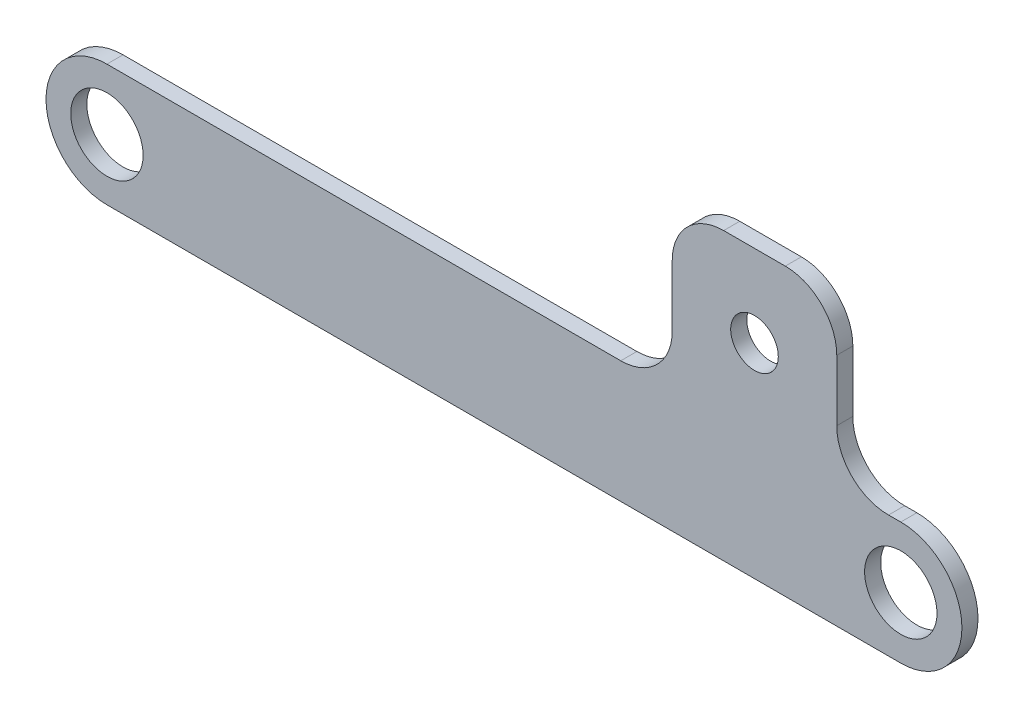
SolidWorks part; units mm, degrees
ref_plane "Front Plane" through (0, 0, 0) normal (0, 0, 1) x (1, 0, 0)
ref_plane "Top Plane" through (0, 0, 0) normal (0, 1, 0) x (1, 0, 0)
ref_plane "Right Plane" through (0, 0, 0) normal (1, 0, 0) x (0, 0, -1)
sketch "Sketch1" plane through (0, 0, 0) normal (0, 0, 1) x (1, 0, 0)
  line L1 (0, -24.13) -> (-313.436, -24.13)
  line L4 (-90.2434, 88.8266) -> (-90.2434, 23.9832)
  line L5 (-90.2434, 23.9832) -> (-313.436, 23.9832)
  line L6 (-25.2863, 23.9832) -> (0, 24.13)
  line L7 (-90.2434, 88.8266) -> (-25.2863, 88.8266)
  line L8 (-25.2863, 88.8266) -> (-25.2863, 23.9832)
  arc A1 (-313.436, -24.13) -> (-313.436, 23.9832) centre (-313.436, -0.0734) cw
  circle A2 centre (-313.436, -0.0734) radius 14.2875
  circle A3 centre (0, 0) radius 14.2875
  circle A4 centre (-57.7649, 56.4783) radius 9.398
  arc A5 (0, -24.13) -> (0, 24.13) centre (0, 0) ccw
  dimension "D1" = 64.8434
  dimension "D2" = 28.575
  dimension "D4" = 18.796
extrude "Boss-Extrude1" add sketch "Sketch1" along normal blind 6.35
fillet "Fillet1" radius 20.32 1 edges at (-90.2434, 23.9832, 3.175)
fillet "Fillet4" radius 20.32 1 edges at (-25.2863, 23.9832, 3.175)
fillet "Fillet5" radius 20.32 1 edges at (-25.2863, 88.8266, 3.175)
fillet "Fillet6" radius 20.32 1 edges at (-90.2434, 88.8266, 3.175)
